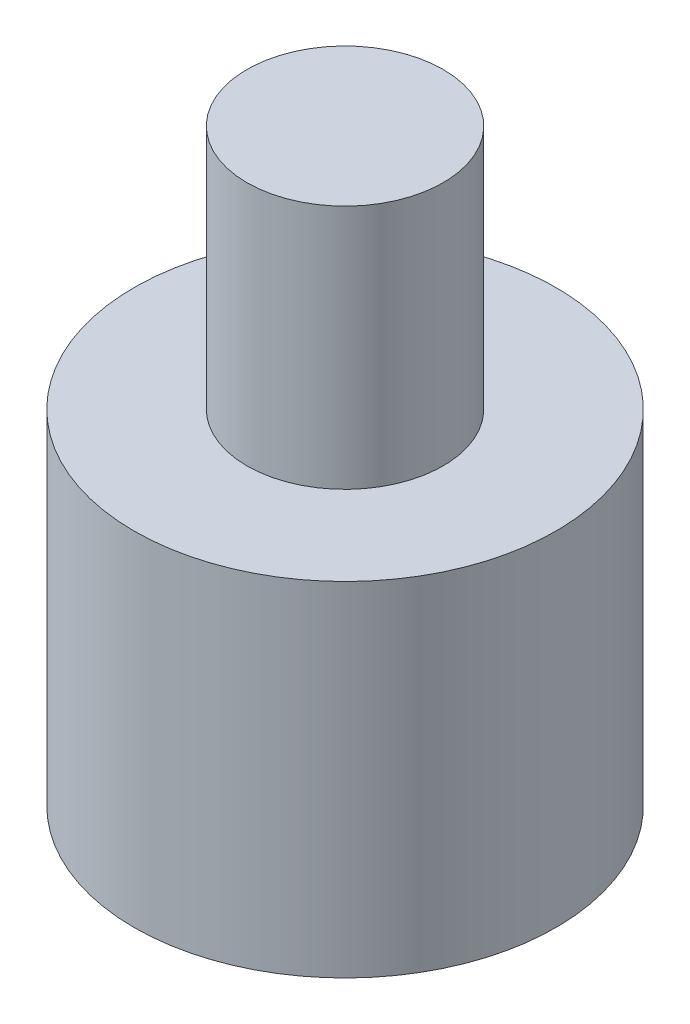
SolidWorks part; units mm, degrees
ref_plane "Front Plane" through (0, 0, 0) normal (0, 0, 1) x (1, 0, 0)
ref_plane "Top Plane" through (0, 0, 0) normal (0, 1, 0) x (1, 0, 0)
ref_plane "Right Plane" through (0, 0, 0) normal (1, 0, 0) x (0, 0, -1)
sketch "Sketch1" plane through (0, 0, 0) normal (0, 1, 0) x (1, 0, 0)
  circle A0 centre (0, 0) radius 2.15
  dimension "D1" = 4.3
extrude "Boss-Extrude1" add sketch "Sketch1" along normal blind 6
sketch "Sketch2" plane through (0, 6, 0) normal (0, 1, 0) x (1, 0, 0)
  circle A0 centre (0, 0) radius 1
  circle A1 centre (0, 0) radius 2.15 construction
  circle A2 centre (0, 0) radius 2.15
  dimension "D1" = 2
extrude "Cut-Extrude1" cut sketch "Sketch2" against normal blind 2.5
sketch "Sketch3" plane through (0, 0, 0) normal (0, -1, 0) x (1, 0, 0)
  point P0 (0, 0)
hole_wizard "M2x0.4 Tapped Hole1" positions "Sketch3" profile "Sketch4" tap size "M2x0.4" standard "ANSI Metric"
sketch "Sketch4" plane through (0, 0, 0) normal (1, 0, 0) x (0, 0, -1)
  line L0 (0, 0) -> (0, 3.9807)
  line L1 (0, 3.9807) -> (0.8, 3.5)
  line L2 (0.8, 3.5) -> (0.8, 0)
  line L5 (0.8, 0) -> (0, 0)
  line L10 (0, 3.9807) -> (-0.8, 3.5) construction
  line L11 (0, -6.35) -> (0, 107.95) construction
  dimension "Tap Drill Dia." = 1.6
  dimension "Tap Drill Depth" = 3.5
  dimension "Drill Angle" = 118
cosmetic thread "Hole Thread1" parameters "D1"=4, "D2"=2
